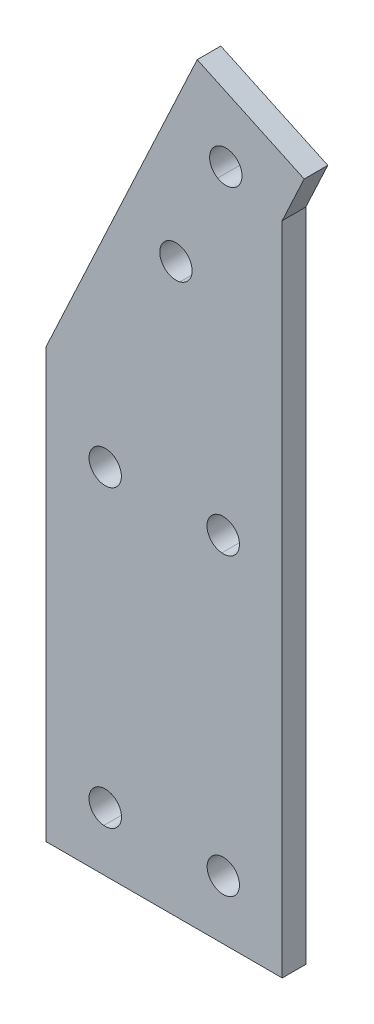
SolidWorks part; units mm, degrees
ref_plane "Front Plane" through (0, 0, 0) normal (0, 0, 1) x (1, 0, 0)
ref_plane "Top Plane" through (0, 0, 0) normal (0, 1, 0) x (1, 0, 0)
ref_plane "Right Plane" through (0, 0, 0) normal (1, 0, 0) x (0, 0, -1)
sketch "Sketch2" plane through (0, 0, 0) normal (0, 0, 1) x (1, 0, 0)
  line L0 (-286.92, -592.342) -> (-286.92, -665.044)
  line L1 (-286.92, -665.044) -> (-246.9204, -665.044)
  line L2 (-246.9204, -665.044) -> (-246.9204, -553.8862)
  line L3 (-246.9204, -553.8862) -> (-243.2021, -545.9123)
  line L4 (-243.2021, -545.9123) -> (-261.328, -537.46)
  line L5 (-261.328, -537.46) -> (-286.92, -592.342)
  line L6 (-286.92, -592.342) -> (-287.145, -591.6661)
  arc A0 (-254.228, -549.178) -> (-257.878, -553.112) centre (-256.48, -550.7488) cw
  arc A1 (-254.228, -549.178) -> (-257.878, -553.112) centre (-256.4808, -550.7481) ccw
  arc A2 (-265.174, -566.142) -> (-264.252, -571.544) centre (-264.9469, -568.8829) cw
  arc A3 (-265.174, -566.142) -> (-264.252, -571.544) centre (-264.9265, -568.8794) ccw
  arc A4 (-256.682, -602.315) -> (-257.159, -607.773) centre (-256.9096, -605.045) cw
  arc A5 (-256.682, -602.315) -> (-257.159, -607.773) centre (-256.9339, -605.0428) ccw
  arc A6 (-276.136, -602.418) -> (-277.476, -607.732) centre (-276.9234, -605.0454) cw
  arc A7 (-276.136, -602.418) -> (-277.476, -607.732) centre (-276.9234, -605.0454) ccw
  arc A8 (-276.92, -652.294) -> (-277.159, -657.773) centre (-276.9141, -655.039) cw
  arc A9 (-276.92, -652.294) -> (-277.159, -657.773) centre (-276.931, -655.0382) ccw
  arc A10 (-256.682, -652.315) -> (-257.159, -657.773) centre (-256.9096, -655.045) cw
  arc A11 (-256.682, -652.315) -> (-257.159, -657.773) centre (-256.9096, -655.045) ccw
  dimension "D1" = 2.7457
  dimension "D2" = 2.7459
  dimension "D3" = 2.7503
  dimension "D4" = 2.7486
  dimension "D5" = 2.7394
  dimension "D6" = 2.7394
  dimension "D7" = 2.7428
  dimension "D8" = 2.745
  dimension "D9" = 2.7443
  dimension "D10" = 2.7394
  dimension "D11" = 243.2021
  dimension "D12" = 246.9204
  dimension "D13" = 254.228
  dimension "D14" = 256.48
  dimension "D15" = 256.4808
  dimension "D16" = 256.682
  dimension "D17" = 256.9096
  dimension "D18" = 256.9339
  dimension "D19" = 264.252
  dimension "D20" = 264.9265
  dimension "D21" = 261.328
  dimension "D22" = 264.9469
  dimension "D23" = 276.9141
  dimension "D24" = 276.92
  dimension "D25" = 276.931
  dimension "D26" = 276.136
  dimension "D27" = 537.46
  dimension "D28" = 545.9123
  dimension "D29" = 276.9234
  dimension "D30" = 549.178
  dimension "D31" = 566.142
  dimension "D32" = 277.476
  dimension "D33" = 286.92
  dimension "D34" = 287.145
  dimension "D35" = 602.315
  dimension "D36" = 602.418
  dimension "D37" = 652.294
  dimension "D38" = 665.044
  dimension "D42" = 591.6661
extrude "Boss-Extrude1" add sketch "Sketch2" along normal blind 4 contours L4 L5 L0 L1 L2 L3 A11 A10 A9 A8 A7 A6 A5 A4 A3 A2 A1 A0
